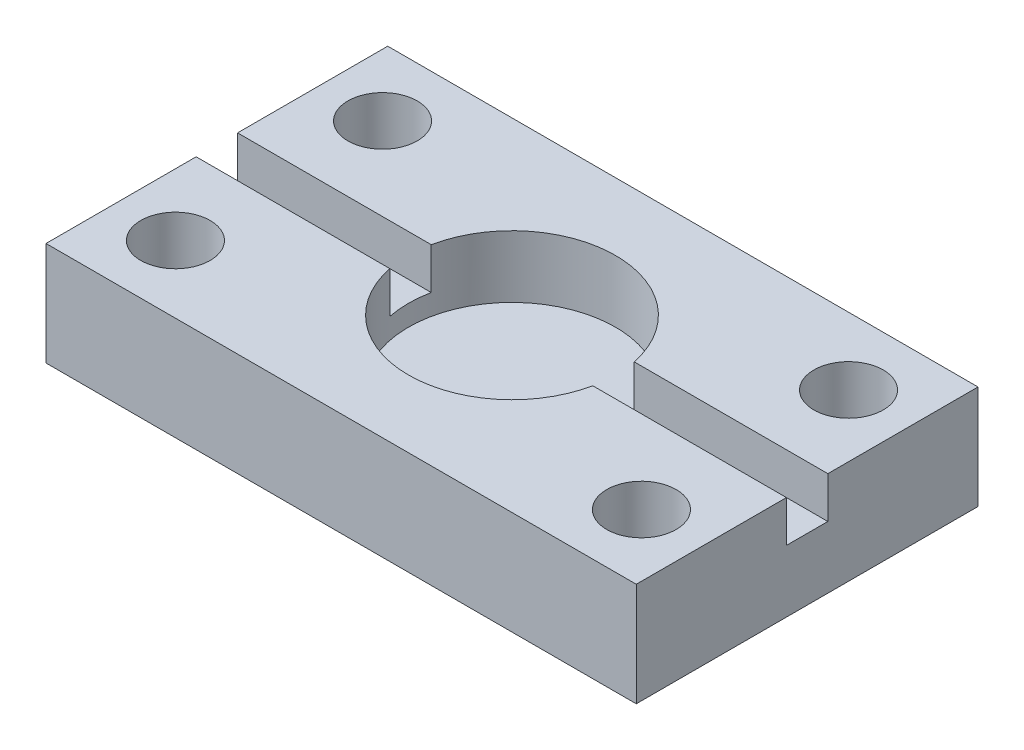
SolidWorks part; units mm, degrees
ref_plane "Front Plane" through (0, 0, 0) normal (0, 0, 1) x (1, 0, 0)
ref_plane "Top Plane" through (0, 0, 0) normal (0, 1, 0) x (1, 0, 0)
ref_plane "Right Plane" through (0, 0, 0) normal (1, 0, 0) x (0, 0, -1)
sketch "Sketch1" plane through (0, 0, 0) normal (0, 1, 0) x (1, 0, 0)
  line L1 (0, 0) -> (57, 0)
  line L2 (0, 0) -> (0, 33)
  line L3 (0, 33) -> (57, 33)
  line L4 (57, 0) -> (57, 33)
  dimension "D1" = 33
  dimension "D2" = 57
extrude "Boss-Extrude1" add sketch "Sketch1" along normal blind 10
sketch "Sketch3" plane through (0, 0, 0) normal (0, -1, 0) x (1, 0, 0)
  line L2 (0, 0) -> (57, 0) construction
  line L3 (0, -33) -> (0, 0) construction
  circle A0 centre (6, -6.5) radius 3.35
  point P4 (28.5, 0)
  point P9 (0, -16.5)
  dimension "D1" = 22.5
  dimension "D3" = 6.7
  dimension "D2" = 10
extrude "Cut-Extrude1" cut sketch "Sketch3" against normal through all
sketch "Sketch4" plane through (0, 0, 0) normal (0, -1, 0) x (1, 0, 0)
  line L2 (57, 0) -> (57, -33) construction
  line L3 (57, -33) -> (0, -33) construction
  circle A0 centre (51, -26.5) radius 3.35
  point P5 (57, -16.5)
  point P10 (28.5, -33)
  dimension "D1" = 10
  dimension "D3" = 6.7
  dimension "D2" = 22.5
extrude "Cut-Extrude2" cut sketch "Sketch4" against normal through all
ref_plane "Plane1" through (0, 0, 0) normal (1, 0, 0) x (0, 0, -1)
sketch "Sketch10" plane through (0, 0, 0) normal (0, -1, 0) x (1, 0, 0)
  line L2 (57, -33) -> (0, -33) construction
  line L3 (57, 0) -> (57, -33) construction
  circle A0 centre (6, -26.5) radius 3.35
  point P5 (28.5, -33)
  point P8 (57, -16.5)
  dimension "D1" = 22.5
  dimension "D3" = 6.7
  dimension "D2" = 10
extrude "Cut-Extrude5" cut sketch "Sketch10" against normal through all
sketch "Sketch12" plane through (0, 0, 0) normal (0, -1, 0) x (1, 0, 0)
  line L2 (57, 0) -> (57, -33) construction
  line L3 (0, 0) -> (57, 0) construction
  circle A0 centre (51, -6.5) radius 3.35
  point P5 (57, -16.5)
  point P10 (28.5, 0)
  dimension "D3" = 6.7
  dimension "D1" = 10
  dimension "D2" = 22.5
extrude "Cut-Extrude6" cut sketch "Sketch12" against normal through all
sketch "Sketch13" plane through (0, 0, -33) normal (0, 0, -1) x (-1, 0, 0)
  line L0 (-28.5, 10) -> (-28.5, 0) construction
  line L1 (-57, 10) -> (0, 10) construction
  line L2 (-57, 0) -> (0, 0) construction
  line L3 (-57, 5) -> (0, 5) construction
  line L4 (-57, 10) -> (-57, 0) construction
sketch "Sketch16" plane through (0, 10, 0) normal (0, 1, 0) x (1, 0, 0)
  line L0 (0, 33) -> (0, 0) construction
  line L1 (0, 18.5) -> (57, 18.5)
  line L2 (0, 18.5) -> (0, 14.5)
  line L3 (0, 14.5) -> (57, 14.5)
  line L4 (57, 18.5) -> (57, 14.5)
  line L5 (57, 0) -> (57, 33) construction
  point P8 (0, 16.5)
  point P9 (0, 16.5)
  dimension "D1" = 4
  dimension "D2" = 0
extrude "Cut-Extrude7" cut sketch "Sketch16" against normal blind 4
sketch "Sketch17" plane through (0, 10, 0) normal (0, 1, 0) x (1, 0, 0)
  line L0 (0, 0) -> (57, 0) construction
  circle A0 centre (28.5, 16.5) radius 10
  point P0 (28.5, 16.5)
  dimension "D1" = 16.5
extrude "Cut-Extrude8" cut sketch "Sketch17" against normal blind 6
